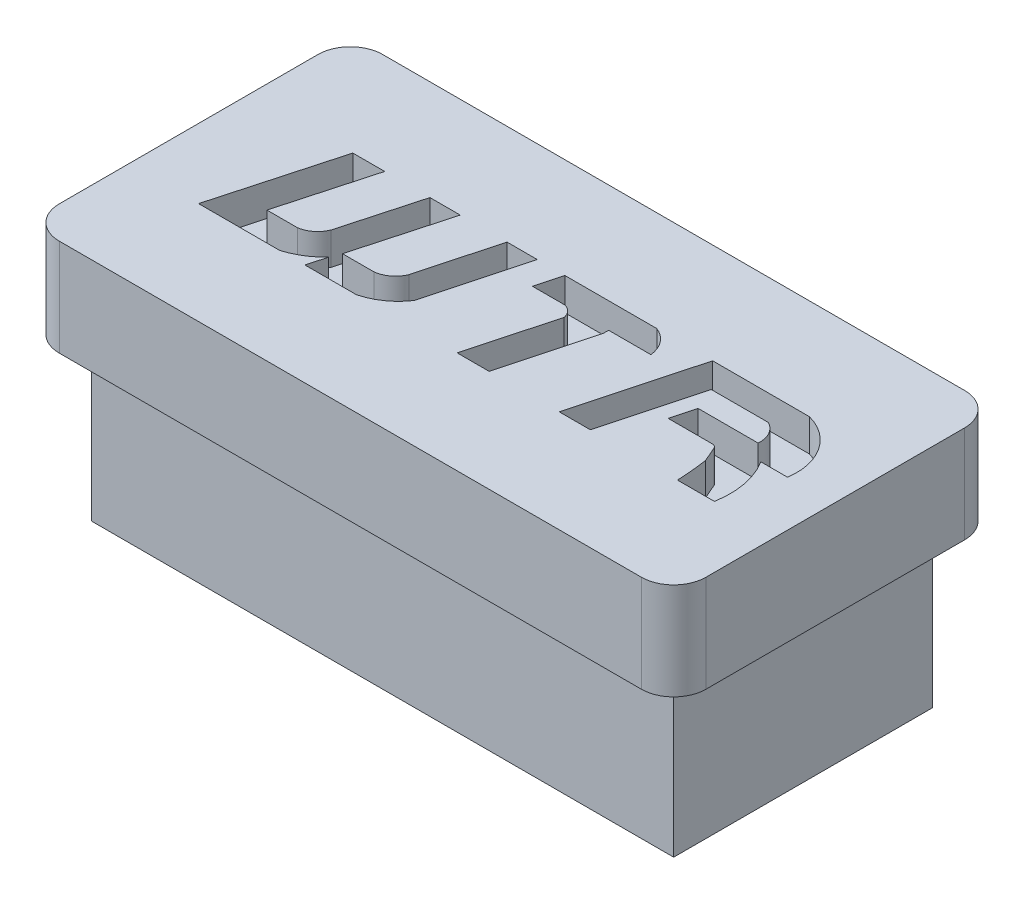
SolidWorks part; units mm, degrees
ref_plane "Front" through (0, 0, 0) normal (0, 0, 1) x (1, 0, 0)
ref_plane "Top" through (0, 0, 0) normal (0, 1, 0) x (1, 0, 0)
ref_plane "Right" through (0, 0, 0) normal (1, 0, 0) x (0, 0, -1)
sketch "草图1" plane through (0, 0, 0) normal (0, 1, 0) x (1, 0, 0)
  line L1 (-10, -5) -> (10, -5)
  line L2 (-10, -5) -> (-10, 5)
  line L3 (-10, 5) -> (10, 5)
  line L4 (10, -5) -> (10, 5)
  line L5 (-10, -5) -> (10, 5) construction
  line L6 (-10, 5) -> (10, -5) construction
  point P0 (0, 0)
extrude "凸台-拉伸1" add sketch "草图1" along normal blind 3
sketch "草图2" plane through (0, 0, 0) normal (0, -1, 0) x (1, 0, 0)
  line L1 (-9, -4) -> (9, -4)
  line L2 (-9, -4) -> (-9, 4)
  line L3 (-9, 4) -> (9, 4)
  line L4 (9, -4) -> (9, 4)
  line L5 (-9, -4) -> (9, 4) construction
  line L6 (-9, 4) -> (9, -4) construction
  point P0 (0, 0)
extrude "凸台-拉伸2" add sketch "草图2" along normal blind 5
fillet "圆角1" radius 1 4 edges at (-10, 1.5, -5) (10, 1.5, -5) (10, 1.5, 5) (-10, 1.5, 5)
sketch "草图5" plane through (0, 3, 0) normal (0, 1, 0) x (1, 0, 0)
  line L0 (-6.8225, 1.8984) -> (-7.8525, -1.8405)
  line L1 (-7.8525, -1.8405) -> (-5.3411, -1.8405)
  line L2 (-4.5651, -1.8405) -> (-2.9707, -1.8405)
  line L3 (-6.8225, 1.8984) -> (-5.8349, 1.8984)
  line L4 (-5.8349, 1.8984) -> (-6.6215, -0.957)
  line L5 (-6.6215, -0.957) -> (-5.6719, -0.957)
  line L6 (-4.4367, 1.8984) -> (-5.0958, -0.4942)
  line L7 (-4.4367, 1.8984) -> (-3.4982, 1.8984)
  line L8 (-3.4982, 1.8984) -> (-4.2848, -0.957)
  line L9 (-4.2848, -0.957) -> (-3.3144, -0.957)
  line L10 (-2.0543, 1.8984) -> (-2.6975, -0.4942)
  line L11 (-2.0543, 1.8984) -> (-1.1158, 1.8984)
  line L12 (-1.1158, 1.8984) -> (-1.9216, -1.0991)
  line L13 (-0.4751, 1.1078) -> (-0.2626, 1.8984)
  line L14 (-0.2626, 1.8984) -> (2.5782, 1.8984)
  line L15 (-0.4751, 1.1078) -> (0.5125, 1.1078)
  line L16 (1.8806, 1.1078) -> (3.1853, 1.1078)
  line L17 (0.1451, -1.8405) -> (0.846, 0.767)
  line L18 (0.1451, -1.8405) -> (1.1334, -1.8405)
  line L19 (1.1334, -1.8405) -> (1.8806, 0.9391)
  line L20 (1.8806, 1.1078) -> (1.8806, 0.9391)
  line L21 (4.307, 1.8984) -> (3.3019, -1.8405)
  line L22 (3.3019, -1.8405) -> (4.2618, -1.8405)
  line L23 (4.2618, -1.8405) -> (5.0544, 1.1078)
  line L24 (5.0544, 1.1078) -> (6.8212, 1.1078)
  line L25 (4.307, 1.8984) -> (7.2998, 1.8984)
  line L26 (7.7604, -0.0623) -> (8.5818, -0.0623)
  line L27 (7.2135, 0.3983) -> (5.3554, 0.3983)
  line L28 (5.3554, 0.3983) -> (5.1591, -0.3318)
  line L29 (5.1591, -0.3318) -> (6.5053, -0.3318)
  line L30 (6.6708, -0.4293) -> (6.864, -0.8758)
  line L31 (6.957, -1.8405) -> (8.0994, -1.8405)
  line L32 (-4.5651, -1.8405) -> (-4.4066, -1.2652)
  arc A0 (-5.6719, -0.957) -> (-5.0958, -0.4942) centre (-5.7912, -0.2185) ccw
  arc A1 (-3.3144, -0.957) -> (-2.6975, -0.4942) centre (-3.4028, -0.1966) ccw
  arc A2 (0.5125, 1.1078) -> (0.846, 0.767) centre (0.4338, 0.6972) cw
  arc A3 (2.5782, 1.8984) -> (3.1853, 1.1078) centre (2.2459, 1.0149) cw
  arc A4 (6.864, -0.8758) -> (6.957, -1.8405) centre (-0.9015, -2.1112) cw
  arc A5 (8.0994, -1.8405) -> (7.7604, -0.0623) centre (5.6117, -1.3933) ccw
  arc A6 (6.6708, -0.4293) -> (6.5053, -0.3318) centre (6.521, -0.4942) ccw
  arc A7 (7.2998, 1.8984) -> (8.5818, -0.0623) centre (6.8509, 0.2054) cw
  arc A8 (-2.9707, -1.8405) -> (-1.9216, -1.0991) centre (-3.4192, -0.0928) ccw
  arc A9 (-5.3411, -1.8405) -> (-4.4066, -1.2652) centre (-5.9637, 0.2174) ccw
  arc A10 (7.2135, 0.3983) -> (6.8212, 1.1078) centre (6.4803, 0.4562) ccw
extrude "切除-拉伸1" cut sketch "草图5" against normal blind 1
